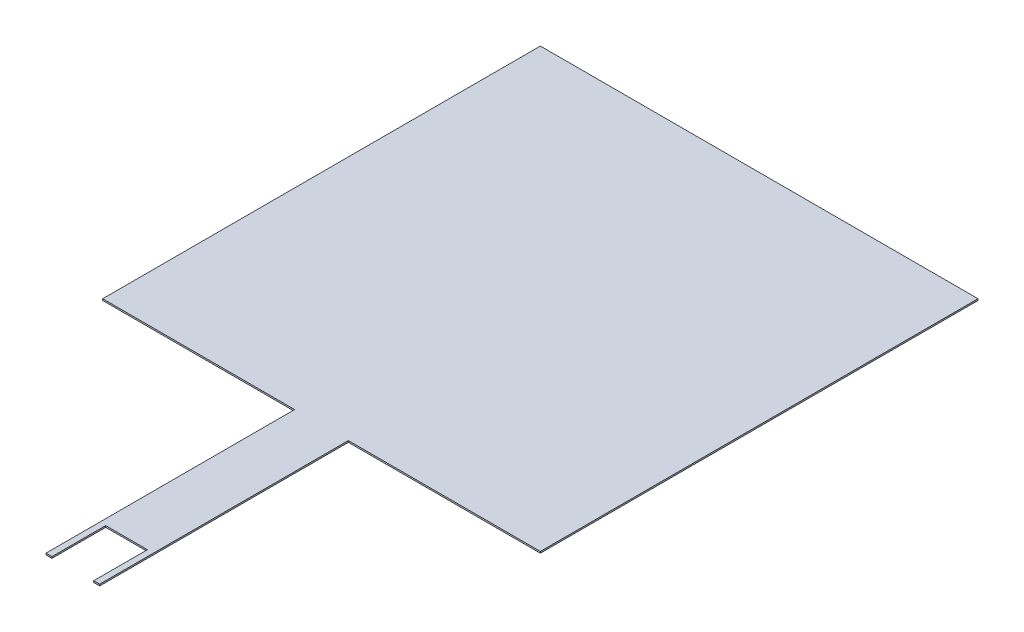
SolidWorks part; units mm, degrees
ref_plane "Front Plane" through (0, 0, 0) normal (0, 0, 1) x (1, 0, 0)
ref_plane "Top Plane" through (0, 0, 0) normal (0, 1, 0) x (1, 0, 0)
ref_plane "Right Plane" through (0, 0, 0) normal (1, 0, 0) x (0, 0, -1)
sketch "Sketch1" plane through (0, 0, 0) normal (0, 1, 0) x (1, 0, 0)
  line L0 (3.429, -27.94) -> (27.94, -27.94)
  line L1 (-27.94, -27.94) -> (-3.429, -27.94)
  line L2 (-27.94, -27.94) -> (-27.94, 27.94)
  line L3 (-27.94, 27.94) -> (27.94, 27.94)
  line L4 (27.94, -27.94) -> (27.94, 27.94)
  line L5 (-27.94, -27.94) -> (27.94, 27.94) construction
  line L6 (-27.94, 27.94) -> (27.94, -27.94) construction
  line L7 (-2.667, -52.832) -> (2.667, -52.832)
  line L8 (-3.429, -52.832) -> (-3.429, -27.94)
  line L10 (3.429, -52.832) -> (3.429, -27.94)
  line L11 (-3.429, -52.832) -> (3.429, -27.94) construction
  line L12 (-3.429, -27.94) -> (3.429, -52.832) construction
  line L14 (-3.429, -52.832) -> (-3.429, -59.69)
  line L15 (-3.429, -59.69) -> (-2.667, -59.69)
  line L16 (-2.667, -52.832) -> (-2.667, -59.69)
  line L18 (3.429, -52.832) -> (3.429, -59.69)
  line L19 (3.429, -59.69) -> (2.667, -59.69)
  line L20 (2.667, -52.832) -> (2.667, -59.69)
  point P0 (0, 0)
  point P6 (0, -40.386)
  dimension "D1" = 55.88
  dimension "D2" = 55.88
  dimension "D3" = 24.892
  dimension "D4" = 6.858
  dimension "D5" = 6.858
  dimension "D6" = 0.762
extrude "Boss-Extrude1" add sketch "Sketch1" along normal blind 0.2032
